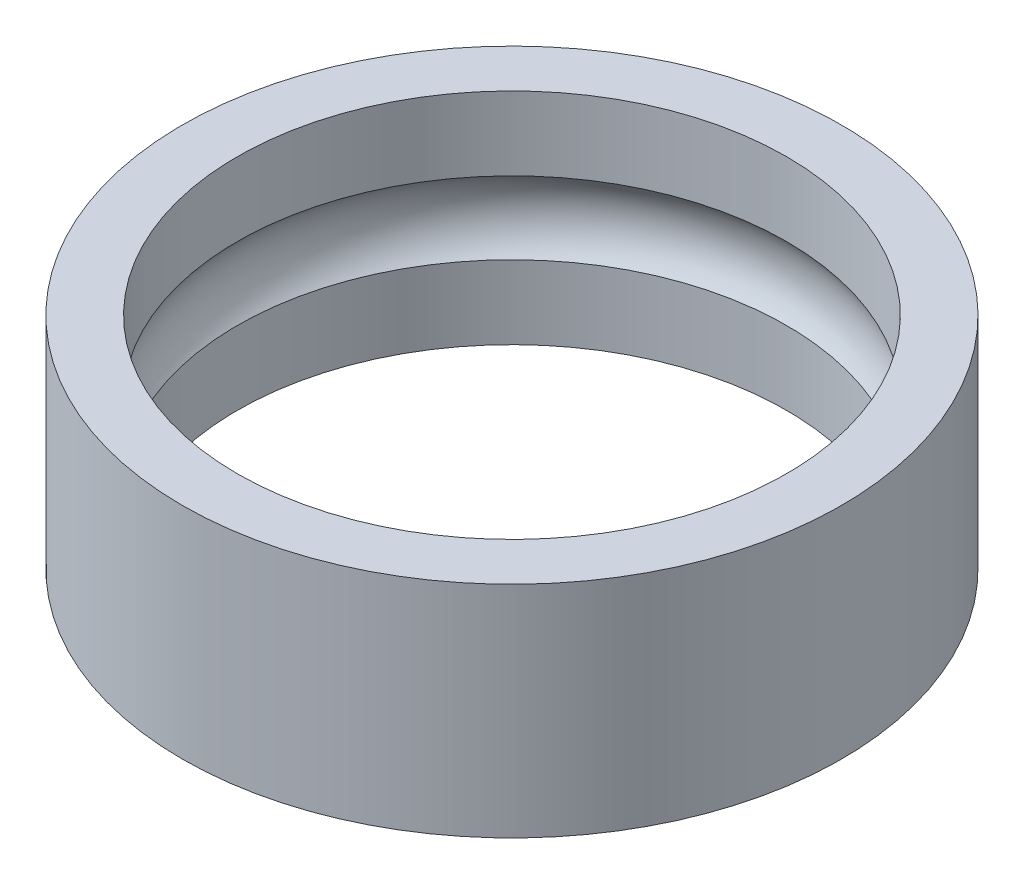
SolidWorks part; units mm, degrees
material "Chrome Stainless Steel"
ref_plane "Front Plane" through (0, 0, 0) normal (0, 0, 1) x (1, 0, 0)
ref_plane "Top Plane" through (0, 0, 0) normal (0, 1, 0) x (1, 0, 0)
ref_plane "Right Plane" through (0, 0, 0) normal (1, 0, 0) x (0, 0, -1)
sketch "DiaProfileS" plane through (0, 0, 0) normal (0, 1, 0) x (1, 0, 0)
  circle A0 centre (0, 0) radius 2.5
  circle A1 centre (0, 0) radius 3
  dimension "InnerDia" = 5
  dimension "Thickness" = 0.5
extrude "DiaProfile" add sketch "DiaProfileS" along normal mid plane 2
sketch "BearingPathProfileS" plane through (0, 0, 0) normal (0, 0, 1) x (1, 0, 0)
  line L1 (0, 0) -> (2.125, 0) construction
  circle A0 centre (2.125, 0) radius 0.5
  point P7 (2.5, 1)
  dimension "BallDia" = 1
  dimension "YDim" = 0.375
  dimension "RefRadius" = 2.125
revolve "BearingPathProfile" cut sketch "BearingPathProfileS" angle 360 about axis through (0, 1, 0) along (0, -1, 0)
